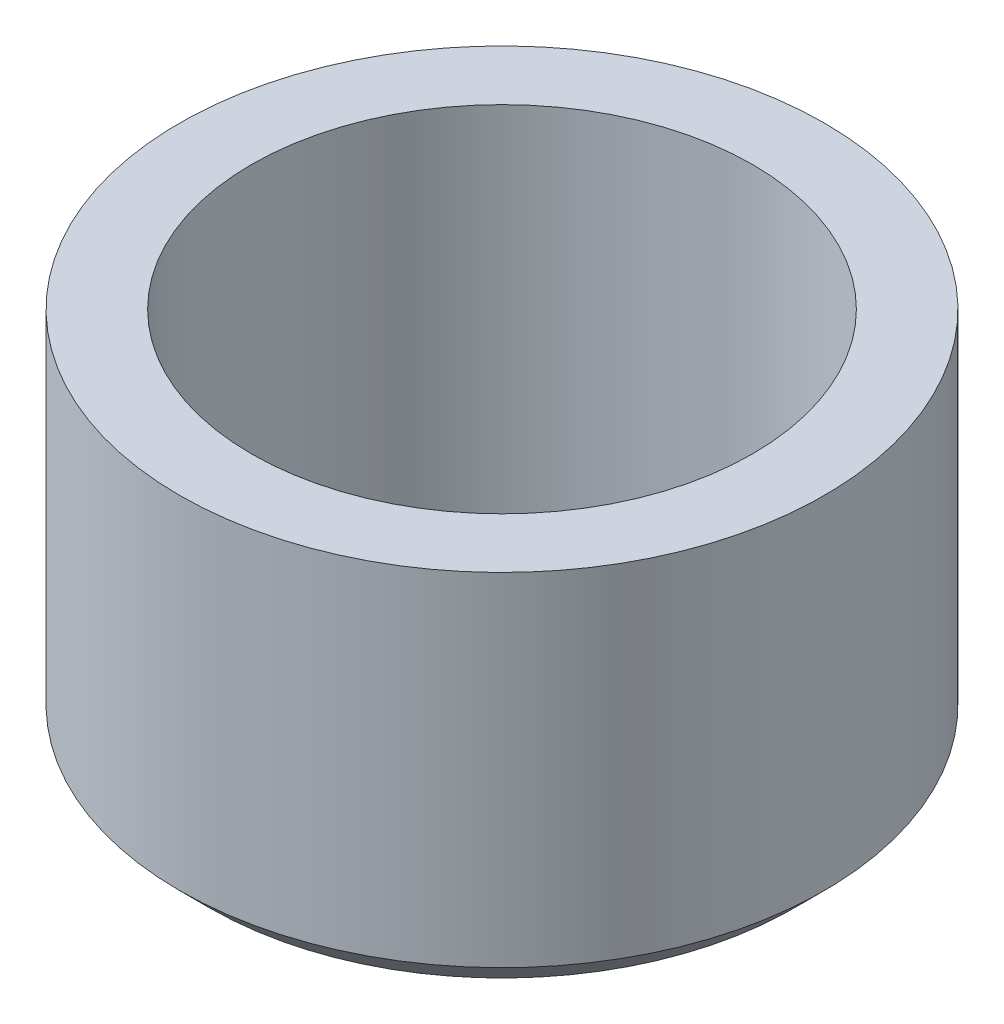
SolidWorks part; units mm, degrees
material "PET"
ref_plane "Front Plane" through (0, 0, 0) normal (0, 0, 1) x (1, 0, 0)
ref_plane "Top Plane" through (0, 0, 0) normal (0, 1, 0) x (1, 0, 0)
ref_plane "Right Plane" through (0, 0, 0) normal (1, 0, 0) x (0, 0, -1)
sketch "Sketch1" plane through (0, 0, 0) normal (0, 0, 1) x (1, 0, 0)
  line L0 (0, 36.0574) -> (0, -35.7852) construction
  line L4 (-5.275, 6.1) -> (-5.275, 0)
  line L5 (-5.275, 0) -> (-4.1, 0)
  line L6 (-4.1, 0) -> (-4.1, 6.1)
  line L7 (-5.275, 6.1) -> (-4.1, 6.1)
  dimension "D1" = 8.2
  dimension "D2" = 6.1
  dimension "D3" = 10.55
revolve "Revolve1" add sketch "Sketch1" angle 360 about L0
chamfer "Chamfer1" distance 0.5 angle 45 1 edges at (0, 0, 5.275)
